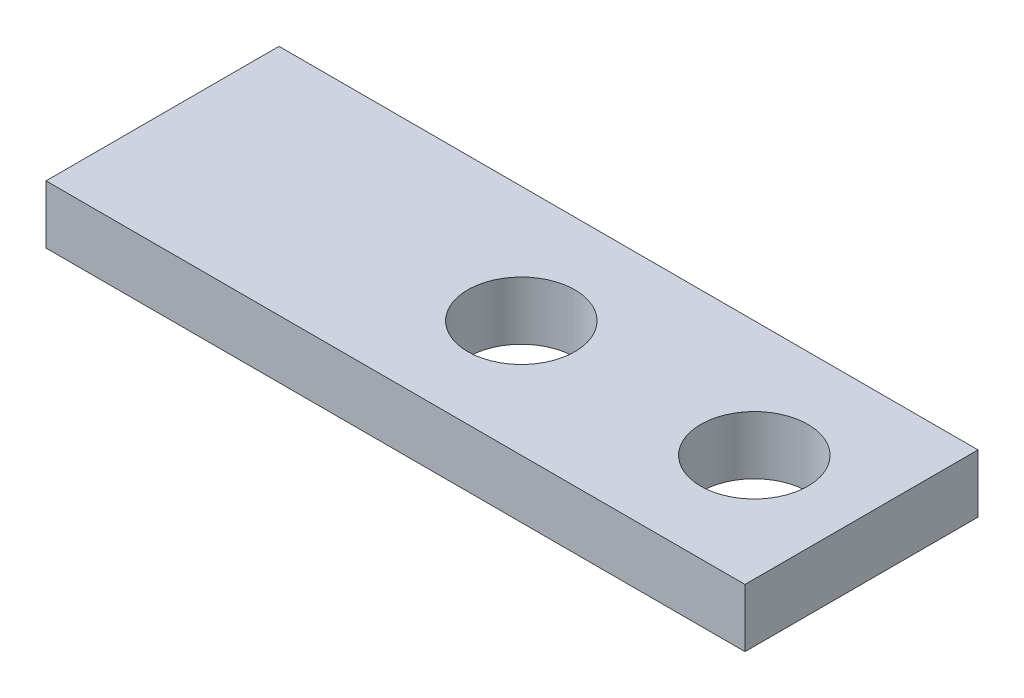
SolidWorks part; units mm, degrees
ref_plane "Front Plane" through (0, 0, 0) normal (0, 0, 1) x (1, 0, 0)
ref_plane "Top Plane" through (0, 0, 0) normal (0, 1, 0) x (1, 0, 0)
ref_plane "Right Plane" through (0, 0, 0) normal (1, 0, 0) x (0, 0, -1)
sketch "Sketch1" plane through (0, 0, 0) normal (0, 1, 0) x (1, 0, 0)
  line L1 (-38.1, -12.7) -> (38.1, -12.7)
  line L2 (-38.1, -12.7) -> (-38.1, 12.7)
  line L3 (-38.1, 12.7) -> (38.1, 12.7)
  line L4 (38.1, -12.7) -> (38.1, 12.7)
  line L5 (-38.1, -12.7) -> (38.1, 12.7) construction
  line L6 (-38.1, 12.7) -> (38.1, -12.7) construction
  circle A0 centre (26.416, 0) radius 5.842
  circle A1 centre (1.016, 0) radius 5.842
  point P0 (0, 0)
  dimension "D3" = 11.684
  dimension "D1" = 76.2
  dimension "D2" = 11.684
  dimension "D4" = 25.4
  dimension "D5" = 25.4
extrude "Boss-Extrude1" add sketch "Sketch1" along normal blind 6.35
